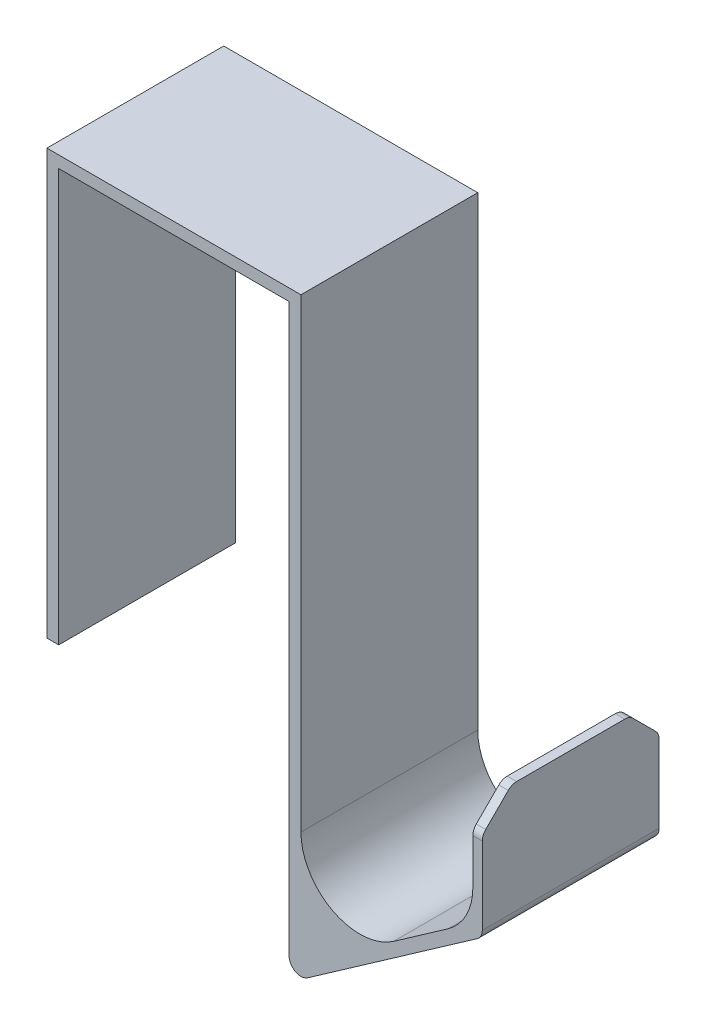
SolidWorks part; units mm, degrees
ref_plane "Plan de face" through (0, 0, 0) normal (0, 0, 1) x (1, 0, 0)
ref_plane "Plan de dessus" through (0, 0, 0) normal (0, 1, 0) x (1, 0, 0)
ref_plane "Plan de droite" through (0, 0, 0) normal (1, 0, 0) x (0, 0, -1)
sketch "Esquisse1" plane through (0, 0, 0) normal (0, 0, 1) x (1, 0, 0)
  line L0 (-19.55, 43.6891) -> (-19.55, 113.6891)
  line L1 (-19.55, 113.6891) -> (19.55, 113.6891)
  line L2 (19.55, 113.6891) -> (19.55, 13.6891)
  line L3 (19.55, 13.6891) -> (52.3161, 36.6321)
  line L4 (52.3161, 36.6321) -> (52.3161, 56.6321)
  line L5 (0, 0) -> (0, 76.9557) construction
  line L6 (-21.55, 43.6891) -> (-21.55, 115.6891)
  line L7 (-21.55, 115.6891) -> (21.55, 115.6891)
  line L8 (21.55, 115.6891) -> (21.55, 17.531)
  line L9 (21.55, 17.531) -> (50.7161, 37.9533)
  line L10 (50.7161, 37.9533) -> (50.7161, 56.6321)
  line L11 (50.7161, 56.6321) -> (52.3161, 56.6321)
  line L12 (-21.55, 43.6891) -> (-19.55, 43.6891)
  point P9 (66.4954, 48.1036)
  point P10 (0, 113.6891)
  point P11 (65.9708, 48.1036)
  point P12 (65.3989, 68.1036)
  dimension "D1" = 39.1
  dimension "D2" = 70
  dimension "D3" = 55
  dimension "D4" = 40
  dimension "D5" = 20
  dimension "D6" = 2
  dimension "D7" = 1.6
  dimension "D8" = 2
  dimension "D9" = 2
  dimension "D10" = 100
  dimension "D11" = 2
extrude "Boss.-Extru.1" add sketch "Esquisse1" along normal blind 30
fillet "Congé1" radius 10 2 edges at (50.7161, 37.9533, 15) (21.55, 17.531, 15)
chamfer "Chanfrein1" distance 5 angle 45 2 edges at (51.5161, 56.6321, 0) (51.5161, 56.6321, 30)
fillet "Congé2" radius 2 6 edges at (52.3161, 36.6321, 15) (19.55, 13.6891, 15) (51.5161, 51.6321, 30) (51.5161, 51.6321, 0) (51.5161, 56.6321, 5) (51.5161, 56.6321, 25)
